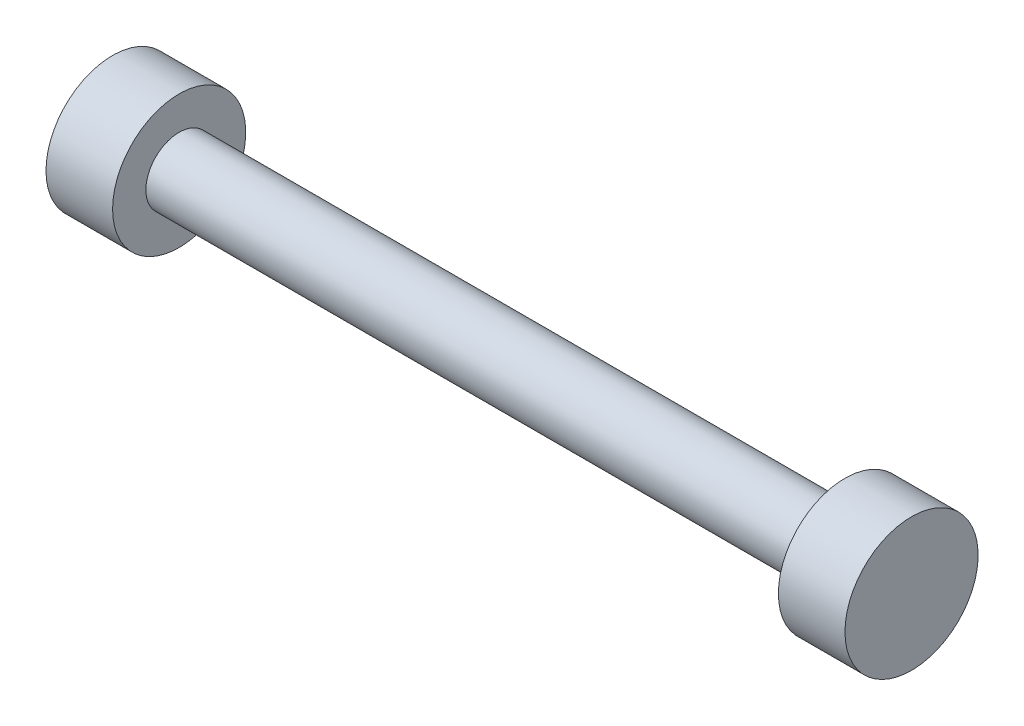
SolidWorks part; units mm, degrees
material "Hierro dúctil"
ref_plane "Alzado" through (0, 0, 0) normal (0, 0, 1) x (1, 0, 0)
ref_plane "Planta" through (0, 0, 0) normal (0, 1, 0) x (1, 0, 0)
ref_plane "Vista lateral" through (0, 0, 0) normal (1, 0, 0) x (0, 0, -1)
sketch "Croquis1" plane through (0, 0, 0) normal (0, 1, 0) x (1, 0, 0)
  line L0 (25, 2.5) -> (25, 5)
  line L3 (-25, 2.5) -> (25, 2.5)
  line L5 (0, 0) -> (25, 2.5) construction
  line L6 (-25, 2.5) -> (0, 0) construction
  line L9 (25, 5) -> (30, 5)
  line L10 (30, 0) -> (30, 5)
  line L11 (0, 5.8824) -> (0, -2.5) construction
  line L12 (-25, 2.5) -> (-25, 5)
  line L14 (-25, 5) -> (-30, 5)
  line L15 (-30, 0) -> (-30, 5)
  line L18 (-39.502, 0) -> (38.9357, 0) construction
  line L19 (-30, 0) -> (30, 0)
  point P0 (0, 0)
  point P6 (30, 0)
  dimension "D1" = 50
  dimension "D2" = 5
  dimension "D3" = 5
revolve "Revolución1" add sketch "Croquis1" angle 360 about L18
